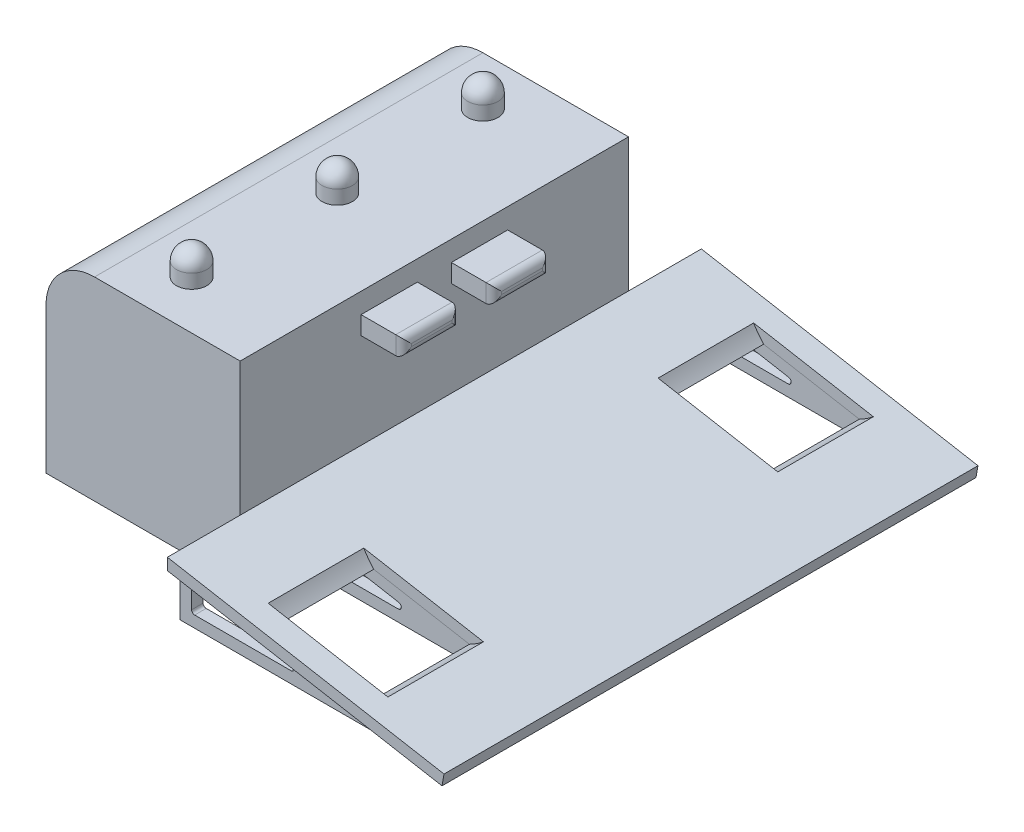
SolidWorks part; units mm, degrees
material "6061 Alloy"
ref_plane "Front Plane" through (0, 0, 0) normal (0, 0, 1) x (1, 0, 0)
ref_plane "Top Plane" through (0, 0, 0) normal (0, 1, 0) x (1, 0, 0)
ref_plane "Right Plane" through (0, 0, 0) normal (1, 0, 0) x (0, 0, -1)
sketch "Sketch1" plane through (0, 0, 0) normal (0, 0, 1) x (1, 0, 0)
  line L1 (-12.7, 50.8) -> (25.4, 50.8)
  line L2 (-25.4, 38.1) -> (-25.4, 0)
  line L3 (-25.4, 0) -> (25.4, 0)
  line L4 (25.4, 50.8) -> (25.4, 0)
  line L5 (-25.4, 50.8) -> (25.4, 0) construction
  line L6 (-25.4, 0) -> (25.4, 50.8) construction
  arc A0 (-12.7, 50.8) -> (-25.4, 38.1) centre (-12.7, 38.1) ccw
  point P0 (0, 25.4)
  dimension "D3" = 12.7
  dimension "D1" = 50.8
  dimension "D2" = 50.8
extrude "Extrude1" add sketch "Sketch1" along normal mid plane 101.6
shell "Shell1" thickness 1.5875
sketch "Sketch2" plane through (0, 50.8, 0) normal (0, 1, 0) x (-1, 0, 0)
  circle A0 centre (0, 0) radius 1.524
  circle A1 centre (0, -38.1) radius 1.524
  circle A2 centre (0, 38.1) radius 1.524
  dimension "D1" = 3.048
  dimension "D3" = 38.1
  dimension "D2" = 38.1
extrude "Extrude2" cut sketch "Sketch2" against normal up to next
sketch "Sketch3" plane through (0, 0, 0) normal (0, 0, 1) x (1, 0, 0)
  line L0 (25.4, 15.875) -> (97.7771, 2.9505)
  line L1 (25.4, 0) -> (25.4, 50.8) construction
  line L2 (114.3, 0) -> (25.4, 0) construction
  line L3 (25.4, 0) -> (25.4, 15.875) construction
  line L4 (25.4, 12.8304) -> (97.2502, 0)
  line L5 (24.8731, 12.9245) -> (113.7731, -2.9505) construction
  line L6 (97.2502, 0) -> (97.7771, 2.9505)
  line L7 (25.4, 15.875) -> (114.3, 0) construction
  line L8 (25.4, 15.875) -> (25.4, 12.8304)
  dimension "D1" = 88.9
  dimension "D2" = 15.875
  dimension "D3" = 2.9972
extrude "Extrude3" add sketch "Sketch3" along normal mid plane 139.7 separate body
ref_plane "Plane1" through (0, 0, 63.5) normal (0, 0, 1) x (1, 0, 0)
sketch "Sketch4" plane through (0, 0, 63.5) normal (0, 0, 1) x (1, 0, 0)
  line L0 (76.7476, 6.7058) -> (45.4316, 12.2979)
  line L1 (-25.4, 0) -> (25.4, 0) construction
  line L3 (25.4, 0) -> (25.4, 50.8) construction
  line L4 (97.7771, 2.9505) -> (25.4, 15.875) construction
  arc A0 (45.4316, 12.2979) -> (76.7476, 6.7058) centre (63.5, 23) ccw
  dimension "D2" = 42
  dimension "D1" = 23
  dimension "D3" = 38.1
extrude "Extrude4" cut sketch "Sketch4" against normal blind 25
mirror "Mirror1" about plane through (0, 0, 0) normal (0, 0, 1) of "Extrude4"
sketch "Sketch5" plane through (25.4, 0, 0) normal (1, 0, 0) x (0, 0, -1)
  line L0 (0, 50.8) -> (0, 0) construction
  line L1 (-19.177, 45.5048) -> (-4.445, 45.5048)
  line L2 (-19.177, 45.5048) -> (-19.177, 40.7423)
  line L3 (-19.177, 40.7423) -> (-4.445, 40.7423)
  line L4 (-4.445, 45.5048) -> (-4.445, 40.7423)
  line L6 (4.445, 45.5048) -> (4.445, 40.7423)
  line L7 (19.177, 40.7423) -> (4.445, 40.7423)
  line L8 (19.177, 45.5048) -> (19.177, 40.7423)
  line L9 (19.177, 45.5048) -> (4.445, 45.5048)
  line L11 (-50.8, 50.8) -> (50.8, 50.8) construction
  line L12 (-69.85, 2.9505) -> (69.85, 2.9505) construction
  dimension "D1" = 14.732
  dimension "D2" = 8.89
  dimension "D3" = 4.7625
  dimension "D4" = 37.7918
extrude "Extrude5" add sketch "Sketch5" along normal blind 11.1125 separate body
fillet "Fillet3" radius 2.032 4 edges at (36.5125, 45.5048, 11.811) (36.5125, 43.1235, 4.445) (36.5125, 40.7423, 11.811) (36.5125, 43.1235, 19.177)
fillet "Fillet4" radius 2.032 4 edges at (36.5125, 43.1235, -19.177) (36.5125, 40.7423, -11.811) (36.5125, 43.1235, -4.445) (36.5125, 45.5048, -11.811)
sketch "Sketch6" plane through (0, 50.8, 0) normal (0, 1, 0) x (1, 0, 0)
  circle A0 centre (0, 38.1) radius 3.9688
  circle A1 centre (0, 0) radius 3.9688
  circle A2 centre (0, -38.1) radius 3.9688
  dimension "D1" = 7.9375
extrude "Extrude6" add sketch "Sketch6" along normal blind 7.62 separate body
fillet "Fillet5" radius 3.9688 1 edges at (0, 58.42, 42.0688)
fillet "Fillet6" radius 3.9688 1 edges at (0, 58.42, 3.9688)
fillet "Fillet7" radius 3.9688 1 edges at (0, 58.42, -34.1313)
sketch "Sketch7" plane through (0, 0, 63.5) normal (0, 0, 1) x (1, 0, 0)
  line L0 (25.4, 12.8304) -> (25.4, 0)
  line L1 (25.4, 0) -> (97.2502, 0)
  line L2 (97.2502, 0) -> (25.4, 12.8304)
  line L3 (54.5952, 4.5723) -> (29.3305, 9.0839)
  line L4 (28.3972, 8.3025) -> (28.3972, 3.7909)
  line L5 (29.1909, 2.9972) -> (54.4557, 2.9972)
  line L6 (63.416, 2.9972) -> (28.3972, 9.2506) construction
  line L7 (28.3972, 2.9972) -> (63.416, 2.9972) construction
  line L8 (28.3972, 9.2506) -> (28.3972, 2.9972) construction
  arc A0 (54.5952, 4.5723) -> (54.4557, 2.9972) centre (54.4557, 3.7909) cw
  arc A1 (29.3305, 9.0839) -> (28.3972, 8.3025) centre (29.1909, 8.3025) ccw
  arc A2 (28.3972, 3.7909) -> (29.1909, 2.9972) centre (29.1909, 3.7909) ccw
  dimension "D2" = 0.7937
  dimension "D3" = 0.7937
  dimension "D1" = 2.9972
extrude "Extrude7" add sketch "Sketch7" along normal blind 2.9972 separate body
sketch "Sketch8" plane through (0, 0, 38.5) normal (0, 0, 1) x (1, 0, 0)
  line L6 (97.2502, 0) -> (25.4, 12.8304)
  line L7 (25.4, 12.8304) -> (25.4, 0)
  line L8 (25.4, 0) -> (97.2502, 0)
  line L9 (97.2502, 0) -> (25.4, 12.8304)
  line L10 (25.4, 12.8304) -> (25.4, 0)
  line L11 (25.4, 0) -> (97.2502, 0)
  line L17 (28.3972, 8.3025) -> (28.3972, 3.7909)
  line L18 (29.1909, 2.9972) -> (54.4557, 2.9972)
  line L19 (28.3972, 8.3025) -> (28.3972, 3.7909)
  line L20 (29.1909, 2.9972) -> (54.4557, 2.9972)
  line L22 (54.5952, 4.5723) -> (29.3305, 9.0839)
  line L23 (54.5952, 4.5723) -> (29.3305, 9.0839)
  arc A6 (29.3305, 9.0839) -> (28.3972, 8.3025) centre (29.1909, 8.3025) ccw
  arc A7 (28.3972, 3.7909) -> (29.1909, 2.9972) centre (29.1909, 3.7909) ccw
  arc A8 (29.3305, 9.0839) -> (28.3972, 8.3025) centre (29.1909, 8.3025) ccw
  arc A9 (28.3972, 3.7909) -> (29.1909, 2.9972) centre (29.1909, 3.7909) ccw
  arc A10 (54.4557, 2.9972) -> (54.5952, 4.5723) centre (54.4557, 3.7909) ccw
  arc A11 (54.4557, 2.9972) -> (54.5952, 4.5723) centre (54.4557, 3.7909) ccw
  dimension "D1" = 0
  dimension "D2" = 0
  dimension "D3" = 0
extrude "Extrude8" add sketch "Sketch8" against normal blind 2.9972 separate body
mirror "Mirror2" about plane through (0, 0, 0) normal (0, 0, 1) of bodies 111 112
